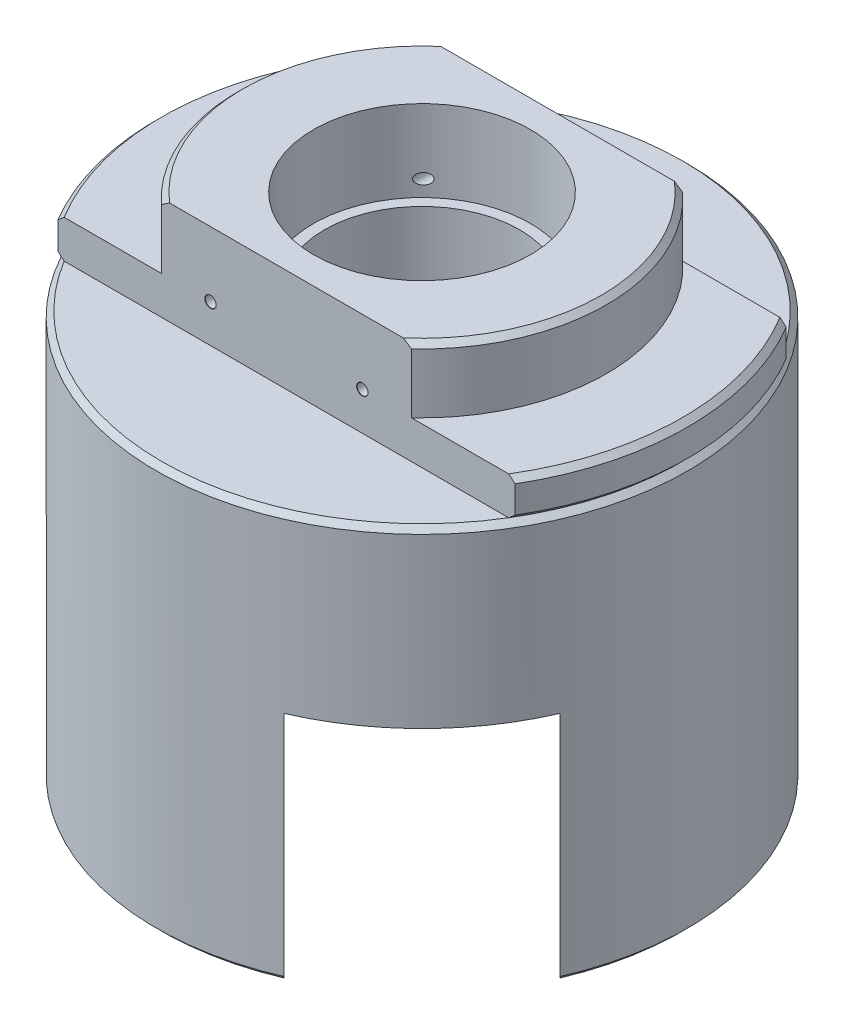
SolidWorks part; units mm, degrees
material "Акрил (Средняя-высокая ударопрочность)"
ref_plane "Спереди" through (0, 0, 0) normal (0, 0, 1) x (1, 0, 0)
ref_plane "Сверху" through (0, 0, 0) normal (0, 1, 0) x (1, 0, 0)
ref_plane "Справа" through (0, 0, 0) normal (1, 0, 0) x (0, 0, -1)
sketch "Эскиз1" plane through (0, 0, 0) normal (0, 1, 0) x (1, 0, 0)
  circle A0 centre (0, 0) radius 24.5
  dimension "D1" = 49
extrude "Бобышка-Вытянуть1" add sketch "Эскиз1" along normal blind 47
sketch "Эскиз2" plane through (0, 47, 0) normal (0, 1, 0) x (1, 0, 0)
  line L0 (-21.0713, 12.5) -> (21.0713, 12.5)
  line L1 (21.0713, -12.5) -> (-21.0713, -12.5)
  circle A0 centre (0, 0) radius 24.5 construction
  circle M1 centre (0, 0) radius 24.5
  dimension "D1" = 25
extrude "Вырез-Вытянуть2" cut sketch "Эскиз2" against normal blind 9.5 contours L0 M1 | L1 M1
sketch "Эскиз4" plane through (0, 47, 0) normal (0, 1, 0) x (1, 0, 0)
  circle A0 centre (0, 0) radius 10
  dimension "D1" = 20
extrude "Вырез-Вытянуть4" cut sketch "Эскиз4" against normal blind 7.5
sketch "Эскиз5" plane through (0, 37.5, 0) normal (0, 1, 0) x (1, 0, 0)
  circle A0 centre (0, 0) radius 17
  dimension "D1" = 34
extrude "Вырез-Вытянуть5" cut sketch "Эскиз5" along normal through all from offset 3.5 flip side to cut
sketch "Эскиз6" plane through (0, 39.5, 0) normal (0, 1, 0) x (1, 0, 0)
  circle A0 centre (0, 0) radius 9
  dimension "D1" = 18
extrude "Вырез-Вытянуть6" cut sketch "Эскиз6" against normal through all
sketch "Эскиз7" plane through (0, 0, 0) normal (0, 0, 1) x (1, 0, 0)
  line L0 (0, 0) -> (0, 47) construction
  line L1 (-9, 0) -> (9, 0) construction
  line L2 (11.5217, 47) -> (-11.5217, 47) construction
  line L3 (0, 32) -> (12, 32)
  line L4 (12, 32) -> (12, 7)
  line L5 (20, 7) -> (20, 0)
  line L6 (12, 7) -> (20, 7)
  line L7 (0, 0) -> (20, 0)
  line L8 (10, 39.5) -> (-10, 39.5) construction
  line L11 (0, 0) -> (0, 32)
  dimension "D1" = 32.5
  dimension "D2" = 24
  dimension "D3" = 40
  dimension "D4" = 25
revolve "Вырез-Повернуть1" cut sketch "Эскиз7" angle 360 about L0
sketch "Эскиз13" plane through (0, 0, 0) normal (0, -1, 0) x (1, 0, 0)
  line L0 (2.8284, 9.8995) -> (7.0711, 5.6569)
  line L1 (7.0711, -5.6569) -> (-2.8284, -15.5563)
  line L2 (-18.3848, -11.3137) -> (-14.1421, -15.5563)
  line L4 (25.85, 0) -> (-25.85, 0) construction
  line L5 (-8.4853, 9.8995) -> (-18.3848, 0)
  arc A0 (-18.3848, 0) -> (-18.3848, -11.3137) centre (-12.7279, -5.6569) ccw
  arc A1 (-14.1421, -15.5563) -> (-2.8284, -15.5563) centre (-8.4853, -9.8995) ccw
  arc A3 (-8.4853, 9.8995) -> (2.8284, 9.8995) centre (-2.8284, 4.2426) cw
  circle A4 centre (0, 0) radius 12 construction
  arc A5 (7.0711, 5.6569) -> (7.0711, -5.6569) centre (1.4142, 0) cw
  dimension "D5" = 8
  dimension "D6" = 13
  dimension "D1" = 22
  dimension "D2" = 21
  dimension "D4" = 45
  dimension "D7" = 30
extrude "Вырез-Вытянуть10" cut sketch "Эскиз13" against normal offset from surface (29.5 mm away) 10
sketch "Эскиз14" plane through (0, 0, 0) normal (0, -1, 0) x (1, 0, 0)
  line L0 (-6.364, 6.364) -> (14.8492, 27.5772)
  line L1 (14.8492, 27.5772) -> (27.5772, 14.8492)
  line L2 (27.5772, 14.8492) -> (6.364, -6.364)
  line L3 (6.364, -6.364) -> (-6.364, 6.364)
  line L5 (-8.4853, 9.8995) -> (-18.3848, 0) construction
  arc M3 (-19.8902, -2.0929) -> (-8.9493, -17.886) centre (0, 0) cw
  circle M5 centre (0, 0) radius 24.5
  dimension "D1" = 18
  dimension "D2" = 30
extrude "Вырез-Вытянуть11" cut sketch "Эскиз14" against normal offset from surface (21.5 mm away) 18 contours L2 L0 M5 M3 | L3 L2 L0 M3 up to face at (0, 39.5, 9)
hole_wizard "Отверстие обработанное метчиком #2-561" positions "Эскиз16" profile "Эскиз15" tap size "#2-56" standard "Ansi (в дюймах)"
sketch "Эскиз16" plane through (0, 7, 0) normal (0, -1, 0) x (1, 0, 0)
  line L4 (0, 0) -> (32.6748, 32.6748) construction
  line L7 (0, 0) -> (-26.4658, 26.4658) construction
  line L11 (-0.7515, 11.9764) -> (9.7489, 22.4768) construction
  point P0 (0, -16.9706)
  point P1 (16.9706, 0)
  point P3 (-16.2635, 5.6569)
  dimension "D1" = 12
  dimension "D2" = 12
  dimension "D3" = 12
  dimension "D4" = 12
  dimension "D5" = 7.5
  dimension "D6" = 15.5
sketch "Эскиз15" plane through (0, 7, -16.9706) normal (1, 0, 0) x (0, 0, -1)
  line L0 (0, 0) -> (0, 10.8075)
  line L1 (0, 10.8075) -> (0.889, 10.2733)
  line L2 (0.889, 10.2733) -> (0.889, 0.2668)
  line L3 (0.889, 0.2668) -> (1.27, 0)
  line L5 (1.27, 0) -> (0, 0)
  line L6 (-0.889, 0.2668) -> (-1.27, 0) construction
  line L10 (0, 10.8075) -> (-0.889, 10.2733) construction
  line L11 (0, -6.35) -> (0, 107.95) construction
  dimension "Диаметр сверла" = 1.778
  dimension "Глубина сверла" = 10.2733
  dimension "Диаметр передней зенковки" = 2.54
  dimension "Угол передней зенковки" = 110
  dimension "Угол заточки сверла" = 118
hole_wizard "Диаметр отверстия Ø2.2 (2.2)1" [suppressed] positions "Эскиз19" profile "Эскиз18" hole size "Ø2.2" standard "DIN"
sketch "Эскиз19" [suppressed] plane through (0, 7, 0) normal (0, -1, 0) x (1, 0, 0)
  line L0 (22.4768, 9.7489) -> (11.9764, -0.7515) construction
  line L1 (11.9764, -0.7515) -> (18.9933, 6.2654) construction
  line L2 (-19.799, -9.8995) -> (-12.7279, -16.9706) construction
  line L3 (-19.799, -9.8995) -> (-12.7279, -16.9706) construction
  point P0 (13.435, -3.5355)
  point P1 (3.5355, -13.435)
  point P3 (8.1317, -15.2028)
  point P5 (15.2028, -8.1317)
  dimension "D1" = 3
  dimension "D2" = 3
  dimension "D3" = 7.5
  dimension "D4" = 7.5
  dimension "D5" = 14
  dimension "D6" = 14
  dimension "D7" = 16
  dimension "D8" = 10
sketch "Эскиз18" plane through (13.435, 7, -3.5355) normal (1, 0, 0) x (0, 0, -1)
  line L0 (0, 0) -> (0, 2.1609)
  line L1 (0, 2.1609) -> (1.1, 1.5)
  line L2 (1.1, 1.5) -> (1.1, 0.1)
  line L3 (1.1, 0.1) -> (1.2, 0)
  line L5 (1.2, 0) -> (0, 0)
  line L6 (-1.1, 0.1) -> (-1.2, 0) construction
  line L10 (0, 2.1609) -> (-1.1, 1.5) construction
  line L11 (0, -6.35) -> (0, 107.95) construction
  dimension "Диаметр отверстия" = 2.2
  dimension "Глубина отверстия" = 1.5
  dimension "Диаметр передней зенковки" = 2.4
  dimension "Угол передней зенковки" = 90
  dimension "Угол заточки сверла" = 118
hole_wizard "Диаметр отверстия Ø1.0 (1)1" positions "Эскиз22" profile "Эскиз23" hole size "Ø1.0" standard "Ansi (метрические)" end condition through all
sketch "Эскиз22" plane through (0, 0, 12.5) normal (0, 0, 1) x (1, 0, 0)
  line L0 (11.5217, 47) -> (-11.5217, 47) construction
  point P0 (-7, 41)
  point P1 (7, 41)
  dimension "D1" = 14
  dimension "D2" = 7
  dimension "D3" = 6
sketch "Эскиз23" plane through (-7, 41, 12.5) normal (1, 0, 0) x (0, -1, 0)
  line L0 (0, 0) -> (0, 25)
  line L1 (0, 25) -> (0.525, 25)
  line L2 (0.5, 24.975) -> (0.5, 0.025)
  line L3 (0.5, 0.025) -> (0.525, 0)
  line L5 (0.525, 0) -> (0, 0)
  line L6 (-0.5, 0.025) -> (-0.525, 0) construction
  line L7 (0.525, 25) -> (0.5, 24.975)
  line L8 (-0.525, 25) -> (-0.5, 24.975) construction
  line L11 (0, -6.35) -> (0, 107.95) construction
  dimension "Диаметр сквозного отверстия" = 1
  dimension "Глубина сквозного отверстия" = 25
  dimension "Диаметр передней зенковки" = 1.05
  dimension "Угол передней зенковки" = 90
  dimension "Диаметр задней зенковки" = 1.05
  dimension "Угол задней зенковки" = 90
sketch "Эскиз24" plane through (0, 0, 0) normal (1, 0, 0) x (0, 0, -1)
  line L0 (0, 0) -> (0, 47) construction
  line L1 (12.5, 47) -> (-12.5, 47) construction
  line L2 (24.5, 37.0001) -> (24.0001, 37.5)
  line L3 (24.5, 0) -> (24.5, 37.5) construction
  line L4 (24.5, 37.5) -> (12.5, 37.5) construction
  line L5 (24.0001, 37.5) -> (24.5, 37.9999)
  line L6 (24.5, 37.9999) -> (24.5, 37.0001)
  dimension "D1" = 45
  dimension "D2" = 0.707
revolve "Вырез-Повернуть2" cut sketch "Эскиз24" angle 360 about L0
chamfer "Фаска1" distance 0.5 angle 45 5 edges at (-17.3241, 0, -17.3241) (-17, 47, 0) (17, 47, 0) (-24.5, 41, 0) (24.5, 41, 0)
